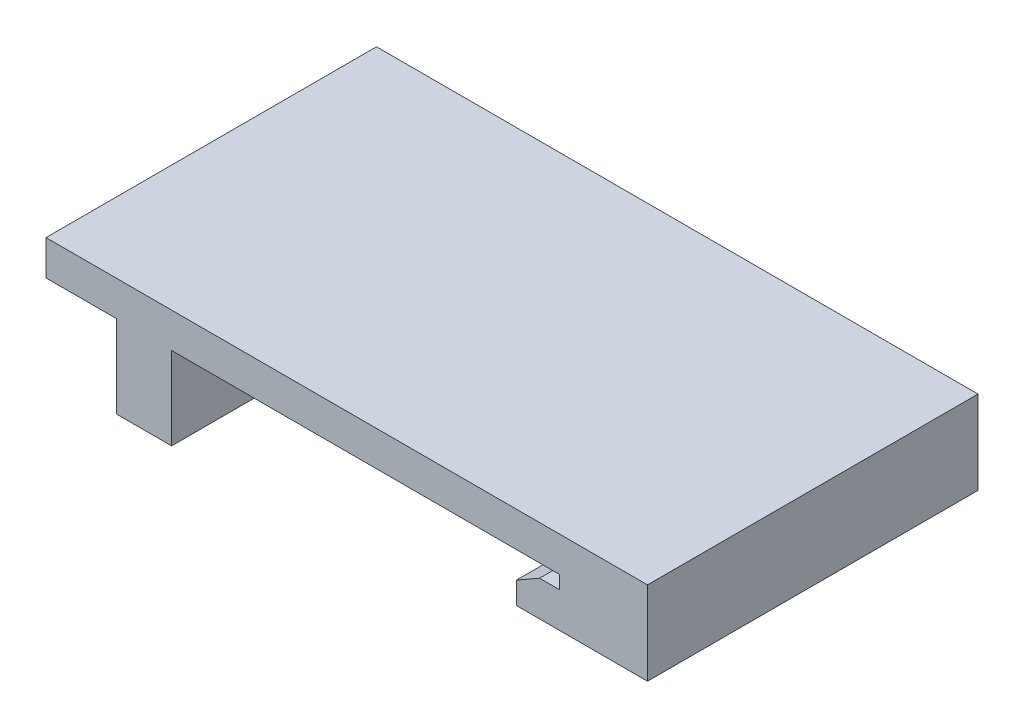
SolidWorks part; units mm, degrees
ref_plane "Front Plane" through (0, 0, 0) normal (0, 0, 1) x (1, 0, 0)
ref_plane "Top Plane" through (0, 0, 0) normal (0, 1, 0) x (1, 0, 0)
ref_plane "Right Plane" through (0, 0, 0) normal (1, 0, 0) x (0, 0, -1)
sketch "Sketch1" plane through (0, 0, 0) normal (0, 0, 1) x (1, 0, 0)
  line L0 (0, 0) -> (19.3, 0)
  line L1 (19.3, 0) -> (19.3, -1.2)
  line L2 (19.3, -1.2) -> (17.5, -1.2)
  line L3 (17.5, -1.2) -> (15.4, -2.4)
  line L4 (15.4, -2.4) -> (15.4, -4.4)
  line L5 (15.4, -4.4) -> (27.3, -4.4)
  line L8 (27.3, 3.175) -> (-27.3, 3.175)
  line L10 (-20.9, -7.5) -> (-15.9, -7.5)
  line L11 (-15.9, -7.5) -> (-15.9, 0)
  line L12 (-15.9, 0) -> (0, 0)
  line L16 (0, 0) -> (0, 6.355) construction
  line L20 (27.3, 3.175) -> (27.3, -4.4)
  line L21 (-27.3, 3.175) -> (-27.3, 0)
  line L22 (-27.3, 0) -> (-20.9, 0)
  line L23 (-20.9, 0) -> (-20.9, -7.5)
  point P10 (0, 0)
  dimension "D2" = 1.8
  dimension "D3" = 3.9
  dimension "D4" = 3.2
  dimension "D5" = 1.2
  dimension "D6" = 1.2
  dimension "D7" = 5
  dimension "D8" = 7.5
  dimension "D9" = 3.175
  dimension "D10" = 15.4
  dimension "D11" = 54.6
  dimension "D14" = 15.9
extrude "Boss-Extrude1" add sketch "Sketch1" along normal blind 30
sketch "Sketch2" plane through (-20.9, 0, 0) normal (-1, 0, 0) x (0, 0, 1)
  line L0 (15, 0) -> (15, -7.5) construction
  line L1 (30, 0) -> (0, 0) construction
  line L2 (30, -7.5) -> (0, -7.5) construction
  line L3 (0, 0) -> (15, 0) construction
  line L4 (7.5, 0) -> (7.5, -7.5) construction
  line L5 (15, 0) -> (30, 0) construction
  line L6 (22.5, 0) -> (22.5, -7.5) construction
  circle A0 centre (7.5, -3.75) radius 1.275
  circle A1 centre (22.5, -3.75) radius 1.275
  point P10 (15, -3.75)
  dimension "D1" = 2.55
extrude "Cut-Extrude1" cut sketch "Sketch2" against normal up to surface (5 mm away) up to face at (-15.9, -3.75, 15)
